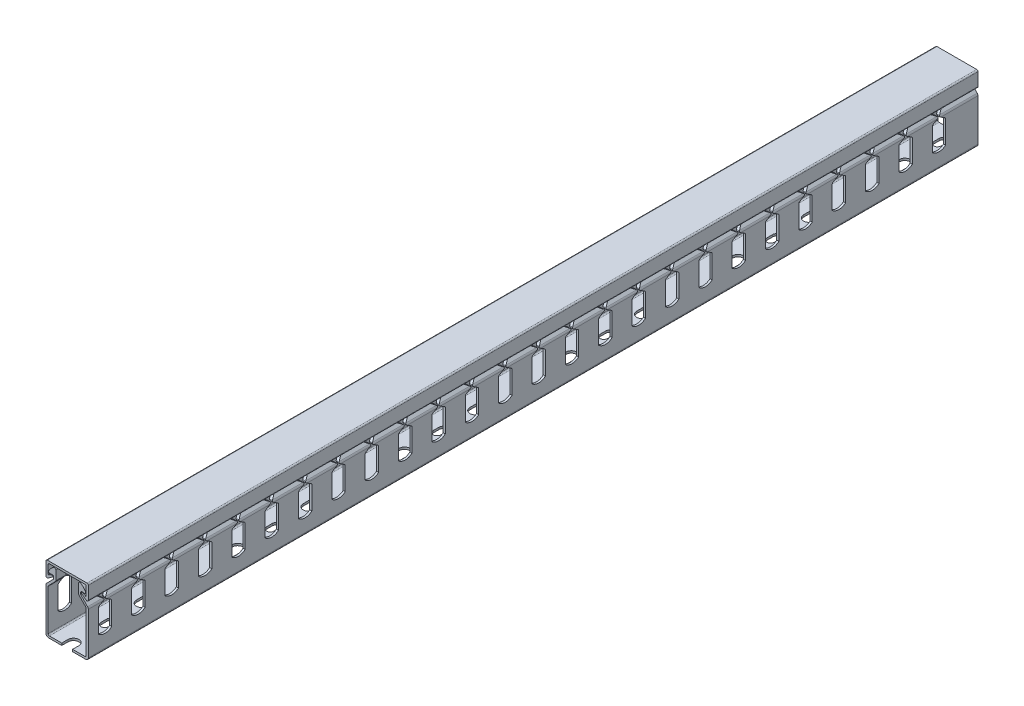
SolidWorks part; units mm, degrees
ref_plane "Front Plane" through (0, 0, 0) normal (0, 0, 1) x (1, 0, 0)
ref_plane "Top Plane" through (0, 0, 0) normal (0, 1, 0) x (1, 0, 0)
ref_plane "Right Plane" through (0, 0, 0) normal (1, 0, 0) x (0, 0, -1)
sketch "Sketch1" plane through (0, 0, 0) normal (0, 0, 1) x (1, 0, 0)
  line L0 (-12.7, 10.6985) -> (12.7, 10.6985) construction
  line L1 (12.7, -20) -> (-12.7, -20) construction
  line L2 (12.7, -20) -> (12.7, 20) construction
  line L3 (12.7, 20) -> (-12.7, 20) construction
  line L4 (-12.7, -20) -> (-12.7, 20) construction
  line L5 (0, 20) -> (0, -20) construction
  line L6 (12.7, 0) -> (-12.7, 0) construction
  line L7 (-12.7, 13.7872) -> (12.7, 13.7872) construction
  line L8 (6.8085, 20) -> (6.8085, 10.6985) construction
  line L9 (-6.8085, 20) -> (6.8085, 10.6985) construction
  line L10 (-6.8085, 20) -> (-6.8085, 10.6985) construction
  line L11 (-12.7, 18.222) -> (12.7, 18.222) construction
  line L12 (-12.7, 13.6284) -> (12.7, 13.6284) construction
  line L13 (-11.4341, 10.8542) -> (-7.685, 13.6284) construction
  line L14 (-10.1877, 13.798) -> (-6.8085, 14.3635) construction
  line L15 (12.7, 7.4) -> (6.8085, 13.4162) construction
  circle A0 centre (-11.9062, 11.4923) radius 0.7938 construction
  circle A1 centre (-10.3187, 14.5809) radius 0.7937 construction
  circle A2 centre (-7.6022, 17.4283) radius 0.7938 construction
  arc A3 (-7.9835, 18.1244) -> (-11.0321, 14.929) centre (-4.4831, 11.7329) ccw construction
  point P0 (0, 0)
  point P4 (11.43, 0)
  point P13 (0, 15.3493)
  point P16 (-11.1125, 13.7872)
  point P21 (-11.1125, 11.4923)
  point P26 (-10.3188, 13.7872)
  point P27 (-10.3188, 13.7872)
  point P28 (-11.1125, 14.5809)
  point P36 (12.7, 7.4)
  dimension "D6" = 7.2873
  dimension "Width" = 25.4
  dimension "Heigth" = 40
  dimension "Wall Thickness" = 1.27
  dimension "Cap Height" = 9.3015
  dimension "Lip Height" = 6.2128
  dimension "D1" = 13.6169
  dimension "D2" = 1.778
  dimension "Lip From Edge" = 1.5875
  dimension "D4" = 0.1588
  dimension "D5" = 36.5
  dimension "D3" = 80.5
  dimension "Shoulder Height" = 27.4
  dimension "D7" = 44.4
sketch "Sketch3" plane through (0, 0, 0) normal (1, 0, 0) x (0, 0, -1)
  line L0 (266.7, 0) -> (-266.7, 0) construction
  line L1 (-266.7, 20) -> (-266.7, -20) construction
  line L2 (-266.7, -20) -> (266.7, -20) construction
  line L3 (266.7, -20) -> (266.7, 20) construction
  line L4 (266.7, 20) -> (-266.7, 20) construction
  line L5 (-252.7, 20) -> (-252.7, 9.8437) construction
  line L6 (-252.7, 9.8437) -> (-256.573, 7.4) construction
  line L7 (-256.573, 7.4) -> (-256.827, 7.4) construction
  line L8 (-256.827, 7.4) -> (-260.7, 9.8437) construction
  line L9 (-260.7, 9.8437) -> (-260.7, 20) construction
  line L10 (-256.827, 7.4) -> (-260.7, 4.9563) construction
  line L11 (-260.7, 4.9563) -> (-260.7, -9.1796) construction
  line L12 (-260.7, -9.1796) -> (-252.7, -9.1796) construction
  line L13 (-252.7, -9.1796) -> (-252.7, 4.9563) construction
  line L14 (-256.573, 7.4) -> (-252.7, 4.9563) construction
  line L15 (-256.7, 7.4) -> (-256.7, -9.1796) construction
  line L16 (-256.7, 7.4) -> (-256.7, 20) construction
  line L17 (-260.7, 4.9563) -> (-252.7, 4.9563) construction
  line L18 (0, 7.4) -> (-256.573, 7.4) construction
  line L19 (-260.7, 9.8437) -> (-260.7, 4.9563) construction
  line L20 (-256.827, 7.4) -> (-260.7, 7.4) construction
  line L21 (-252.7, 4.9563) -> (-240.7, 4.9563) construction
  line L22 (-240.7, 4.9563) -> (-232.7, 4.9563) construction
  line L23 (-236.7, 4.9563) -> (-236.7, -9.1796) construction
  line L24 (-139.7, 20) -> (-139.7, -20) construction
  line L25 (139.7, 20) -> (139.7, -20) construction
  arc A0 (-260.7, -9.1796) -> (-252.7, -9.1796) centre (-256.7, -4.7075) ccw construction
  circle A1 centre (-257.5707, 7.4) radius 0.3969 construction
  circle A2 centre (-255.8293, 7.4) radius 0.3969 construction
  point P29 (-232.7, 4.9563)
  point P30 (-240.7, 4.9563)
  point P31 (-240.7, 4.9563)
  point P32 (-236.7, 4.9563)
  point P34 (-139.7, 0)
  point P39 (139.7, 0)
  dimension "D2" = 6
  dimension "D6" = 0.7937
  dimension "Length" = 533.4
  dimension "Side Cut Out Width" = 8
  dimension "D3" = 6
  dimension "D1" = 10.8204
  dimension "D4" = 64.5
  dimension "D5" = 0.254
  dimension "Cut Spacing" = 12
  dimension "Cut Center To Center" = 20
  dimension "D7" = 127
  dimension "D8" = 127
sketch "Sketch4" plane through (0, 0, 0) normal (0, 1, 0) x (1, 0, 0)
  line L0 (0, -270.45) -> (0, -262.95) construction
  line L1 (-12.7, 266.7) -> (12.7, 266.7) construction
  line L2 (-12.7, 266.7) -> (-12.7, -266.7) construction
  line L3 (-12.7, -266.7) -> (12.7, -266.7) construction
  line L4 (12.7, 266.7) -> (12.7, -266.7) construction
  line L5 (0, -266.7) -> (0, 266.7) construction
  line L6 (-12.7, 0) -> (12.7, 0) construction
  line L7 (-3.25, -270.45) -> (-3.25, -262.95) construction
  line L8 (3.25, -270.45) -> (3.25, -262.95) construction
  line L9 (0, -244.2) -> (0, -240.7) construction
  line L10 (-2.25, -244.2) -> (-2.25, -240.7) construction
  line L11 (2.25, -244.2) -> (2.25, -240.7) construction
  line L12 (0, -221.95) -> (0, -214.45) construction
  line L13 (-3.25, -221.95) -> (-3.25, -214.45) construction
  line L14 (3.25, -221.95) -> (3.25, -214.45) construction
  line L15 (0, -191.45) -> (0, -194.95) construction
  line L16 (2.25, -191.45) -> (2.25, -194.95) construction
  line L17 (-2.25, -191.45) -> (-2.25, -194.95) construction
  line L18 (-12.7, -139.7) -> (12.7, -139.7) construction
  line L19 (-12.7, 139.7) -> (12.7, 139.7) construction
  arc A0 (-3.25, -270.45) -> (3.25, -270.45) centre (0, -270.45) ccw construction
  arc A1 (3.25, -262.95) -> (-3.25, -262.95) centre (0, -262.95) ccw construction
  arc A2 (-2.25, -244.2) -> (2.25, -244.2) centre (0, -244.2) ccw construction
  arc A3 (2.25, -240.7) -> (-2.25, -240.7) centre (0, -240.7) ccw construction
  arc A4 (-3.25, -221.95) -> (3.25, -221.95) centre (0, -221.95) ccw construction
  arc A5 (3.25, -214.45) -> (-3.25, -214.45) centre (0, -214.45) ccw construction
  arc A6 (2.25, -191.45) -> (-2.25, -191.45) centre (0, -191.45) ccw construction
  arc A7 (-2.25, -194.95) -> (2.25, -194.95) centre (0, -194.95) ccw construction
  point P0 (0, 0)
  point P5 (0, -266.7)
  point P13 (0, -242.45)
  point P18 (0, -238.45)
  point P19 (0, -246.45)
  point P20 (0, -259.7)
  point P21 (0, -273.7)
  point P24 (0, -218.2)
  point P31 (0, -193.2)
  point P40 (0, -225.2)
  point P41 (0, -211.2)
  dimension "Large Hole Radius" = 3.25
  dimension "Large Hole Length" = 14
  dimension "Slot With" = 8
  dimension "End Hole Spacing" = 48.5
  dimension "D4" = 24.25
  dimension "Hole Spacing" = 25
  dimension "Mounting Hole Diameter" = 4.5
sketch "Sketch5" plane through (0, 0, 0) normal (0, 0, 1) x (1, 0, 0)
  line L0 (-6.8085, 17.4283) -> (-6.8085, 11.6011)
  line L1 (-6.8085, 20) -> (-6.8085, 10.6985) construction
  line L2 (-6.8085, 11.6011) -> (-11.43, 6.8817)
  line L3 (-11.43, 6.8817) -> (-11.43, -18.73)
  line L4 (-11.43, -18.73) -> (11.43, -18.73)
  line L5 (11.43, -18.73) -> (11.43, 6.8817)
  line L6 (11.43, 6.8817) -> (6.8085, 11.6011)
  line L7 (6.8085, 11.6011) -> (6.8085, 17.4283)
  line L8 (6.8085, 20) -> (6.8085, 10.6985) construction
  line L9 (12.7, 7.4) -> (6.8085, 13.4162) construction
  line L10 (0, 20) -> (0, -20) construction
  line L11 (11.43, 0) -> (12.7, 0) construction
  line L12 (8.0785, 12.1194) -> (6.8085, 12.1194) construction
  line L13 (-10.1877, 13.798) -> (-6.8085, 14.3635) construction
  line L14 (-10.1877, 13.798) -> (-8.0785, 14.151)
  line L15 (-8.0785, 14.151) -> (-8.0785, 12.1194)
  line L16 (-8.0785, 12.1194) -> (-12.7, 7.4)
  line L17 (-12.7, -20) -> (-12.7, 20) construction
  line L18 (-12.7, 7.4) -> (-12.7, -20)
  line L19 (-12.7, -20) -> (12.7, -20)
  line L20 (12.7, -20) -> (12.7, 7.4)
  line L21 (12.7, 7.4) -> (8.0785, 12.1194)
  line L22 (8.0785, 12.1194) -> (8.0785, 14.151)
  line L23 (6.8085, 12.1194) -> (-6.8085, 12.1194) construction
  line L24 (-6.8085, 12.1194) -> (-8.0785, 12.1194) construction
  line L25 (11.43, 6.8817) -> (12.3374, 7.7703) construction
  line L26 (-12.7, 18.222) -> (12.7, 18.222) construction
  line L27 (10.1877, 13.798) -> (8.0785, 14.151)
  line L28 (11.43, -18.73) -> (11.43, -20) construction
  line L29 (-12.7, 20) -> (-12.7, 11.4923)
  line L30 (-12.7, 20) -> (12.7, 20)
  line L31 (-11.4341, 10.8542) -> (-8.7512, 12.8395)
  line L32 (-11.4341, 10.8542) -> (-7.685, 13.6284) construction
  line L33 (12.7, 20) -> (12.7, 11.4923)
  line L34 (12.7, -20) -> (12.7, 20) construction
  line L35 (8.7512, 12.8395) -> (11.4341, 10.8542)
  line L36 (-12.7, 10.6985) -> (12.7, 10.6985) construction
  line L37 (-11.43, 12.4371) -> (-11.43, 18.73)
  line L38 (-11.43, 18.73) -> (11.43, 18.73)
  line L39 (11.43, 18.73) -> (11.43, 12.4371)
  line L40 (-11.43, 18.73) -> (-11.43, 20) construction
  line L41 (-11.43, 18.73) -> (-12.7, 18.73) construction
  line L42 (-11.43, 12.4371) -> (-10.6707, 12.999)
  line L43 (-11.0503, 12.7181) -> (-10.2949, 11.6972) construction
  line L44 (-8.9869, 13.5542) -> (-8.9869, 13.158) construction
  line L45 (10.6707, 12.999) -> (11.43, 12.4371)
  line L46 (10.6707, 12.999) -> (9.9153, 11.9781) construction
  circle A0 centre (-7.6022, 17.4283) radius 0.7938 construction
  arc A1 (-7.9835, 18.1244) -> (-11.0321, 14.929) centre (-4.4831, 11.7329) ccw construction
  arc A2 (-7.9835, 18.1244) -> (-11.0321, 14.929) centre (-4.4831, 11.7329) ccw
  circle A3 centre (-10.3187, 14.5809) radius 0.7937 construction
  arc A4 (-11.0321, 14.929) -> (-10.1877, 13.798) centre (-10.3187, 14.5809) ccw
  arc A5 (-6.8085, 17.4283) -> (-7.9835, 18.1244) centre (-7.6022, 17.4283) ccw
  arc A6 (7.9835, 18.1244) -> (6.8085, 17.4283) centre (7.6022, 17.4282) ccw
  arc A7 (10.1877, 13.798) -> (11.0321, 14.929) centre (10.3187, 14.5809) ccw
  arc A8 (7.9835, 18.1244) -> (11.0321, 14.929) centre (4.4831, 11.7329) cw
  circle A9 centre (-11.9062, 11.4923) radius 0.7938 construction
  arc A10 (-12.7, 11.4923) -> (-11.4341, 10.8542) centre (-11.9062, 11.4923) ccw
  arc A11 (11.4341, 10.8542) -> (12.7, 11.4923) centre (11.9062, 11.4923) ccw
  arc A12 (-8.7512, 12.8395) -> (-8.9869, 13.5542) centre (-8.9869, 13.158) ccw
  arc A13 (-10.6707, 12.999) -> (-8.9869, 13.5542) centre (-8.9869, 10.7234) cw
  arc A14 (8.7512, 12.8395) -> (8.9869, 13.5542) centre (8.9869, 13.158) cw
  arc A15 (8.9869, 13.5542) -> (10.6707, 12.999) centre (8.9869, 10.7234) cw
  point P10 (0, -18.73)
  point P81 (0, 18.73)
  dimension "D2" = 0.3962
  dimension "D1" = 3.3376
extrude "Boss-Extrude1" add sketch "Sketch5" along normal up to vertex (266.7 mm away) and the other way up to vertex (266.7 mm away) up to point (0, -20, 266.7) other way up to point (0, -20, -266.7)
fillet "Fillet1" radius 0.254 2 edges at (-11.43, 12.4371, 0) (11.43, 12.4371, 0)
fillet "Fillet2" radius 0.7937 4 edges at (12.7, 20, 0) (11.43, 18.73, 0) (-11.43, 18.73, 0) (-12.7, 20, 0)
fillet "Fillet3" radius 1.5875 4 edges at (-12.7, -20, 0) (12.7, -20, 0) (12.7, 7.4, 0) (-12.7, 7.4, 0)
fillet "Fillet4" radius 0.7937 8 edges at (-11.43, -18.73, 0) (11.43, -18.73, 0) (8.0785, 14.151, 0) (-8.0785, 14.151, 0) (-11.43, 6.8817, 0) (-6.8085, 11.6011, 0) (6.8085, 11.6011, 0) (11.43, 6.8817, 0)
sketch "Sketch6" plane through (0, 0, 0) normal (1, 0, 0) x (0, 0, -1)
  line L0 (-260.7, 20) -> (-260.7, 10.2814)
  line L1 (-260.7, 4.9563) -> (-260.7, -9.1796) construction
  line L2 (-256.827, 7.4) -> (-260.7, 4.9563) construction
  line L3 (-252.7, -9.1796) -> (-252.7, 4.9563) construction
  line L4 (-256.573, 7.4) -> (-252.7, 4.9563) construction
  line L5 (-252.7, 9.8437) -> (-256.573, 7.4) construction
  line L6 (-252.7, 20) -> (-252.7, 9.8437) construction
  line L7 (-256.827, 7.4) -> (-260.7, 9.8437) construction
  line L8 (-260.7, 4.5186) -> (-260.7, -9.1796)
  line L9 (-257.359, 7.0644) -> (-260.3298, 5.1899)
  line L10 (-252.7, -9.1796) -> (-252.7, 4.5186)
  line L11 (-256.041, 7.0644) -> (-253.0702, 5.1899)
  line L12 (-253.0702, 9.6101) -> (-256.041, 7.7356)
  line L13 (-252.7, 20) -> (-252.7, 10.2814)
  line L14 (-257.359, 7.7356) -> (-260.3298, 9.6101)
  line L15 (-252.7, 20) -> (-260.7, 20)
  circle A0 centre (-255.8293, 7.4) radius 0.3969 construction
  circle A1 centre (-257.5707, 7.4) radius 0.3969 construction
  arc A2 (-256.041, 7.7356) -> (-256.041, 7.0644) centre (-255.8293, 7.4) ccw
  arc A3 (-257.359, 7.0644) -> (-257.359, 7.7356) centre (-257.5707, 7.4) ccw
  arc A4 (-260.7, -9.1796) -> (-252.7, -9.1796) centre (-256.7, -4.7075) ccw construction
  arc A5 (-260.7, -9.1796) -> (-252.7, -9.1796) centre (-256.7, -4.7075) ccw
  arc A6 (-253.0702, 9.6101) -> (-252.7, 10.2814) centre (-253.4937, 10.2814) ccw
  arc A7 (-252.7, 4.5186) -> (-253.0702, 5.1899) centre (-253.4937, 4.5186) ccw
  arc A8 (-260.7, 4.5186) -> (-260.3298, 5.1899) centre (-259.9062, 4.5186) cw
  arc A9 (-260.7, 10.2814) -> (-260.3298, 9.6101) centre (-259.9062, 10.2814) ccw
  dimension "D1" = 0.7937
extrude "Cut-Extrude2" cut sketch "Sketch6" against normal through all both and the other way through all
pattern_linear "LPattern2" count 26 spacing 20 along (0, 0, -1) of "Cut-Extrude2"
sketch "Sketch7" plane through (0, -20, 0) normal (0, -1, 0) x (1, 0, 0)
  line L0 (-3.25, 270.45) -> (-3.25, 262.95) construction
  line L1 (3.25, 270.45) -> (3.25, 262.95) construction
  line L2 (-3.25, 270.45) -> (-3.25, 262.95)
  line L3 (3.25, 270.45) -> (3.25, 262.95)
  line L4 (-2.25, 244.2) -> (-2.25, 240.7) construction
  line L5 (2.25, 244.2) -> (2.25, 240.7) construction
  line L6 (-2.25, 244.2) -> (-2.25, 240.7)
  line L7 (2.25, 244.2) -> (2.25, 240.7)
  arc A0 (3.25, 270.45) -> (-3.25, 270.45) centre (0, 270.45) ccw construction
  arc A1 (-3.25, 262.95) -> (3.25, 262.95) centre (0, 262.95) ccw construction
  arc A2 (3.25, 270.45) -> (-3.25, 270.45) centre (0, 270.45) ccw
  arc A3 (-3.25, 262.95) -> (3.25, 262.95) centre (0, 262.95) ccw
  arc A4 (2.25, 244.2) -> (-2.25, 244.2) centre (0, 244.2) ccw construction
  arc A5 (-2.25, 240.7) -> (2.25, 240.7) centre (0, 240.7) ccw construction
  arc A6 (2.25, 244.2) -> (-2.25, 244.2) centre (0, 244.2) ccw
  arc A7 (-2.25, 240.7) -> (2.25, 240.7) centre (0, 240.7) ccw
extrude "Cut-Extrude3" cut sketch "Sketch7" against normal up to vertex (1.27 mm away) up to point (10.6363, -18.73, 266.7)
sketch "Sketch8" plane through (0, -20, 0) normal (0, -1, 0) x (1, 0, 0)
  line L0 (-2.25, 191.45) -> (-2.25, 194.95) construction
  line L1 (2.25, 191.45) -> (2.25, 194.95) construction
  line L2 (3.25, 221.95) -> (3.25, 214.45) construction
  line L3 (-3.25, 221.95) -> (-3.25, 214.45) construction
  line L4 (-2.25, 191.45) -> (-2.25, 194.95)
  line L5 (2.25, 191.45) -> (2.25, 194.95)
  line L6 (3.25, 221.95) -> (3.25, 214.45)
  line L7 (-3.25, 221.95) -> (-3.25, 214.45)
  arc A0 (-2.25, 191.45) -> (2.25, 191.45) centre (0, 191.45) ccw construction
  arc A1 (2.25, 194.95) -> (-2.25, 194.95) centre (0, 194.95) ccw construction
  arc A2 (3.25, 221.95) -> (-3.25, 221.95) centre (0, 221.95) ccw construction
  arc A3 (-3.25, 214.45) -> (3.25, 214.45) centre (0, 214.45) ccw construction
  arc A4 (-2.25, 191.45) -> (2.25, 191.45) centre (0, 191.45) ccw
  arc A5 (2.25, 194.95) -> (-2.25, 194.95) centre (0, 194.95) ccw
  arc A6 (3.25, 221.95) -> (-3.25, 221.95) centre (0, 221.95) ccw
  arc A7 (-3.25, 214.45) -> (3.25, 214.45) centre (0, 214.45) ccw
extrude "Cut-Extrude4" cut sketch "Sketch8" against normal up to vertex
pattern_linear "LPattern3" count 12 spacing 50 along (0, 0, -1) of "Cut-Extrude4"
equation "\"D2@Sketch1\"=\"Wall Thickness@Sketch1\"*1.4"
equation "\"D4@Sketch1\"=\"Wall Thickness@Sketch1\"*.125"
equation "\"D2@Sketch3\" = \"Side Cut Out Width@Sketch3\" * .75"
equation "\"D4@Sketch4\" = \"End Hole Spacing@Sketch4\" / 2"
equation "\"D3@LPattern2\"=\"Cut Center To Center@Sketch3\""
equation "\"D1@LPattern2\"=\"Length@Sketch3\"/\"Cut Center To Center@Sketch3\"-1"
equation "\"D1@LPattern3\"=(\"Length@Sketch3\"/50mm)+1"
equation "\"D7@Sketch3\"=\"D8@Sketch3\""
